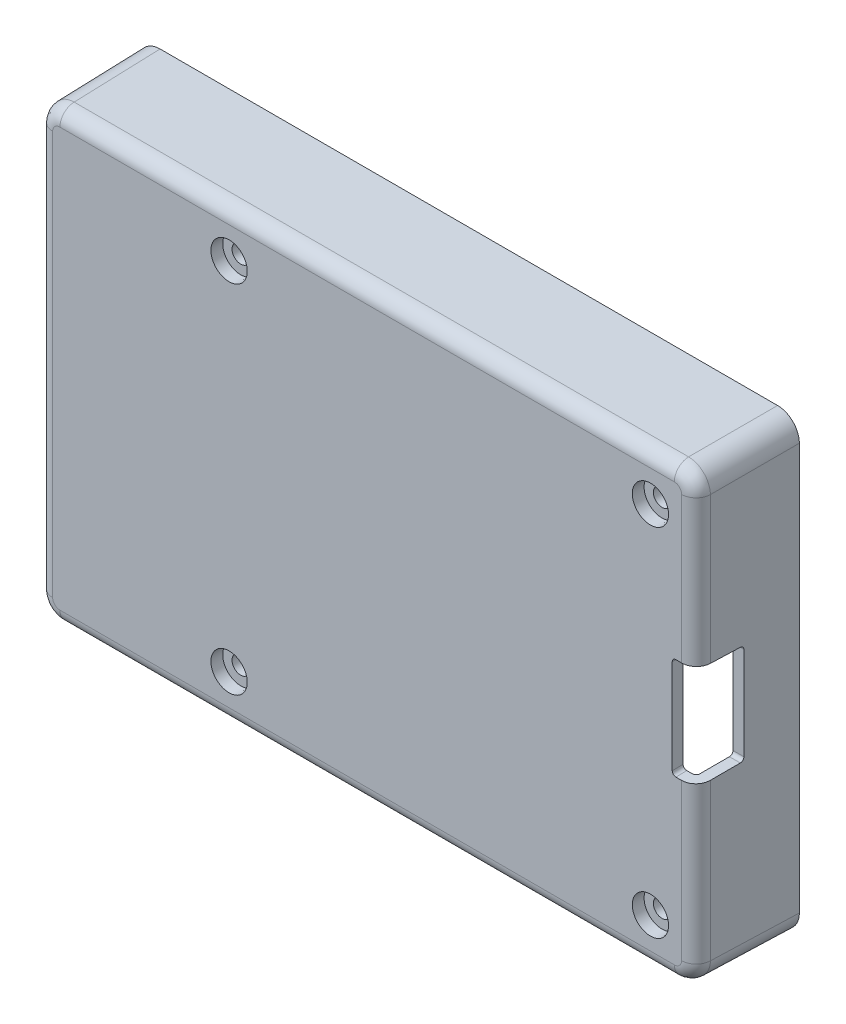
SolidWorks part; units mm, degrees
ref_plane "Front" through (0, 0, 0) normal (0, 0, 1) x (1, 0, 0)
ref_plane "Top" through (0, 0, 0) normal (0, 1, 0) x (1, 0, 0)
ref_plane "Right" through (0, 0, 0) normal (1, 0, 0) x (0, 0, -1)
sketch "Sketch1" plane through (0, 0, 0) normal (0, 0, 1) x (1, 0, 0)
  circle A0 centre (-19, 24.5) radius 3.5
  circle A1 centre (39, 24.5) radius 3.5
  circle A2 centre (-19, -24.5) radius 3.5
  circle A3 centre (39, -24.5) radius 3.5
  dimension "D1" = 7
extrude "Standoffs" add sketch "Sketch1" along normal blind 6 draft 1 draft outward yes
sketch "Sketch2" plane through (0, 0, 6) normal (0, 0, 1) x (1, 0, 0)
  line L1 (-45.5, 31) -> (45.5, 31)
  line L2 (-45.5, 31) -> (-45.5, -31)
  line L3 (-45.5, -31) -> (45.5, -31)
  line L4 (45.5, 31) -> (45.5, -31)
  line L5 (-45.5, 31) -> (45.5, -31) construction
  line L6 (-45.5, -31) -> (45.5, 31) construction
  line L9 (-40, 28) -> (40, 28) construction
  line L10 (42.5, 25.5) -> (42.5, -25.5) construction
  point P0 (0, 0)
  dimension "D1" = 3
  dimension "D2" = 3
extrude "Base" add sketch "Sketch2" against normal blind 1.5
sketch "Sketch3" plane through (0, 0, 4.5) normal (0, 0, -1) x (-1, 0, 0)
  line L0 (-44, 29.5) -> (-44, -29.5)
  line L1 (-44, -29.5) -> (44, -29.5)
  line L2 (44, -29.5) -> (44, 29.5)
  line L3 (44, 29.5) -> (-44, 29.5)
  line L4 (-45.5, 31) -> (-45.5, -31)
  line L5 (-45.5, -31) -> (45.5, -31)
  line L6 (45.5, -31) -> (45.5, 31)
  line L7 (45.5, 31) -> (-45.5, 31)
  line L8 (-45.5, 31) -> (-45.5, -31)
  line L9 (-45.5, -31) -> (45.5, -31)
  line L10 (45.5, -31) -> (45.5, 31)
  line L11 (45.5, 31) -> (-45.5, 31)
  dimension "D1" = 0
  dimension "D2" = 1.5
extrude "Walls" add sketch "Sketch3" along normal blind 12.5
hole_wizard "CBORE for M2 Pan Head Machine Screw1" positions "Sketch5" profile "Sketch6" counterbore size "M2" standard "ANSI Metric" end condition through all
sketch "Sketch5" plane through (0, 0, 6) normal (0, 0, 1) x (1, 0, 0)
  point P0 (39, -24.5)
  point P2 (-19, -24.5)
  point P4 (39, 24.5)
  point P6 (-19, 24.5)
sketch "Sketch6" plane through (39, -24.5, 6) normal (1, 0, 0) x (0, -1, 0)
  line L0 (0, 0) -> (0, 14)
  line L1 (0, 14) -> (1.2, 14)
  line L3 (1.2, 14) -> (1.2, 1.6)
  line L4 (1.2, 1.6) -> (2.5, 1.6)
  line L5 (2.5, 1.6) -> (2.5, 0)
  line L7 (2.5, 0) -> (0, 0)
  line L11 (0, -6.35) -> (0, 107.95) construction
  dimension "Thru Hole Dia." = 2.4
  dimension "Thru Hole Depth" = 14
  dimension "C'Bore Dia." = 5
  dimension "C'Bore Depth" = 1.6
sketch "Sketch7" plane through (0, 0, 0) normal (1, 0, 0) x (0, 0, -1)
  line L4 (1.6, -26) -> (15.8, -26)
  line L5 (15.8, -26) -> (15.8, -8.696)
  line L6 (15.8, -8.696) -> (1.6, -8.696)
  line L7 (1.6, -8.696) -> (1.6, -26)
  line L8 (1.6, -26) -> (15.8, -26)
  line L9 (15.8, -26) -> (15.8, -8.696)
  line L10 (15.8, -8.696) -> (1.6, -8.696)
  line L11 (1.6, -8.696) -> (1.6, -26)
  line L12 (0.81, -6.14) -> (17.3, -6.14)
  line L13 (17.3, -6.14) -> (17.3, 8.64)
  line L14 (17.3, 8.64) -> (0.81, 8.64)
  line L15 (0.81, 8.64) -> (0.81, -6.14)
  line L16 (0.81, -6.14) -> (17.3, -6.14)
  line L17 (17.3, -6.14) -> (17.3, 8.64)
  line L18 (17.3, 8.64) -> (0.81, 8.64)
  line L19 (0.81, 8.64) -> (0.81, -6.14)
  line L20 (0.81, 11.4) -> (17.3, 11.4)
  line L21 (17.3, 11.4) -> (17.3, 26.3)
  line L22 (17.3, 26.3) -> (0.81, 26.3)
  line L23 (0.81, 26.3) -> (0.81, 11.4)
  line L24 (0.81, 11.4) -> (17.3, 11.4)
  line L25 (17.3, 11.4) -> (17.3, 26.3)
  line L26 (17.3, 26.3) -> (0.81, 26.3)
  line L27 (0.81, 26.3) -> (0.81, 11.4)
  dimension "D1" = 0
  dimension "D2" = 0
  dimension "D3" = 0
extrude "USB and Ethernet Cut" cut sketch "Sketch7" against normal through all
sketch "Sketch8" plane through (0, 0, 0) normal (0, 1, 0) x (1, 0, 0)
  line L0 (10.2, 7.8) -> (10.2, 2.215) construction
  line L1 (12.32, 7.8) -> (8.08, 7.8) construction
  line L2 (10.075, 2.215) -> (10.325, 2.215) construction
  line L3 (2.7, 6.2) -> (2.7, 7) construction
  line L4 (2.2, 1.3) -> (18.2, 1.3)
  line L5 (2.2, 1.3) -> (2.2, 8.715)
  line L6 (2.2, 8.715) -> (18.2, 8.715)
  line L7 (18.2, 1.3) -> (18.2, 8.715)
  line L8 (2.2, 1.3) -> (18.2, 8.715) construction
  line L9 (2.2, 8.715) -> (18.2, 1.3) construction
  line L10 (31.75, 4.1369) -> (31.75, 1.3) construction
  line L11 (34.75, 4.1369) -> (28.75, 4.1369) construction
  line L12 (-40, 1.3) -> (40, 1.3) construction
  line L13 (28.01, 2.6036) -> (28.01, 3.35) construction
  line L14 (27.51, 0.8075) -> (35.99, 0.8075)
  line L15 (27.51, 0.8075) -> (27.51, 4.6294)
  line L16 (27.51, 4.6294) -> (35.99, 4.6294)
  line L17 (35.99, 0.8075) -> (35.99, 4.6294)
  line L18 (27.51, 0.8075) -> (35.99, 4.6294) construction
  line L19 (27.51, 4.6294) -> (35.99, 0.8075) construction
  line L20 (28.75, 4.1294) -> (34.75, 4.1294) construction
  line L21 (-14.4, 4.3) -> (-14.4646, 8)
  line L22 (45.5, 8) -> (-45.5, 8) construction
  line L23 (-14.4646, 8) -> (-7.3354, 8)
  line L24 (-10.9, 8) -> (-10.9, 4.3) construction
  line L25 (-7.4, 4.3) -> (-7.3354, 8)
  line L26 (27.51, 4.6294) -> (27.51, 8)
  line L27 (27.51, 8) -> (35.99, 8)
  line L28 (35.99, 8) -> (35.99, 4.6294)
  circle A0 centre (-10.9, 4.3) radius 3.5
  arc A1 (-9.9633, 7.15) -> (-11.8367, 7.15) centre (-10.9, 4.3) ccw construction
  point P12 (10.2, 5.0075)
  point P26 (31.75, 2.7184)
  dimension "D1" = 0.5
  dimension "D2" = 0.5
  dimension "D3" = 1.3
  dimension "D4" = 0.5
  dimension "D5" = 0.5
  dimension "D6" = 89
extrude "Side Ports" cut sketch "Sketch8" against normal through all contours L28 L27 L26 L16 | L14 L17 L16 L15 | L4 L7 L6 L5 | A0 L25 L23 L21 | A0 L23
draft "Draft2" type of draft neutral plane draft angle 1 faces to draft 4 face at (0, 31, -1) face at (-45.5, 0.688, -3.6525) face at (45.5, 0, -1) face at (7.7625, -31, -3.8322) neutral plane through (0, 0, -8) neutral plane normal (0, 0, -1) reverse direction yes parameters "D1"=1
draft "Draft3" type of draft neutral plane draft angle 1 faces to draft 4 face at (44, 0, -1.75) face at (0, 29.5, -1.75) face at (-44, 0.688, -3.84) face at (7.7625, -29.5, -4.0197) neutral plane through (0, 0, -8) neutral plane normal (0, 0, -1) parameters "D1"=1
fillet "Fillet1" radius 3 4 edges at (-45.3778, 30.8778, -1) (-45.3778, -30.8778, -1) (45.3778, 30.8778, -1) (45.3778, -30.8778, -1)
fillet "Fillet2" radius 1.5 4 edges at (-43.8909, -29.3909, -1.75) (-43.8909, 29.3909, -1.75) (43.8909, 29.3909, -1.75) (43.8909, -29.3909, -1.75)
fillet "Fillet3" radius 2 8 edges at (-44.3771, -29.8771, 6) (-45.2556, 0, 6) (-44.3771, 29.8771, 6) (0, 30.7556, 6) (44.3771, 29.8771, 6) (45.2556, 0, 6) (44.3771, -29.8771, 6) (0, -30.7556, 6)
fillet "Fillet4" radius 0.5 12 edges at (-15.4215, 24.5, 4.5) (42.5785, 24.5, 4.5) (-15.4215, -24.5, 4.5) (42.5785, -24.5, 4.5) (43.3426, -28.8426, 4.5) (43.7818, 0, 4.5) (43.3426, 28.8426, 4.5) (0, 29.2818, 4.5) (-43.3426, 28.8426, 4.5) (-43.7818, 0, 4.5) (-43.3426, -28.8426, 4.5) (0, -29.2818, 4.5)
sketch "Sketch10" plane through (0, 0, 0) normal (1, 0, 0) x (0, 0, -1)
  line L0 (-0.65, 7.2) -> (-0.65, -5.8) construction
  line L1 (-1.3, 7.2) -> (0, 7.2) construction
  line L2 (-1.3, -5.8) -> (0, -5.8) construction
  line L3 (-1.3, 7.2) -> (-1.3, -5.8) construction
  line L4 (0.5, -6.3) -> (-1.8, -6.3)
  line L5 (0.5, -6.3) -> (0.5, 7.7)
  line L6 (0.5, 7.7) -> (-1.8, 7.7)
  line L7 (-1.8, -6.3) -> (-1.8, 7.7)
  line L8 (0.5, -6.3) -> (-1.8, 7.7) construction
  line L9 (0.5, 7.7) -> (-1.8, -6.3) construction
  line L10 (-1.8, 7.7) -> (-6, 7.7)
  line L11 (-6, -30.7556) -> (-6, 30.7556) construction
  line L12 (-6, 7.7) -> (-6, -6.3)
  line L13 (-6, -6.3) -> (-1.8, -6.3)
  point P6 (-0.65, 0.7)
  dimension "D1" = 0.5
  dimension "D2" = 0.5
extrude "SD Card" cut sketch "Sketch10" along normal through all from offset 42 contours L7 L4 L5 L6 | L12 L13 L7 L10
draft "Draft4" type of draft neutral plane draft angle 1 faces to draft 10 face at (2.2, -30.1915, -4.65) face at (27.51, -30.1872, -4.4038) face at (35.99, -30.1872, -4.4038) face at (18.2, -30.1915, -4.65) face at (-44.6941, -26, -4.8) face at (-44.6872, -6.14, -4.405) face at (-44.6872, 11.4, -4.405) face at (-44.6941, -8.696, -4.8) face at (-44.6872, 8.64, -4.405) face at (-44.6872, 26.3, -4.405) neutral plane through (0, 0, -8) neutral plane normal (0, 0, -1) parameters "D1"=1
draft "Draft7" type of draft neutral plane draft angle 1 faces to draft 2 face at (43.6752, -6.3, 3.5694) face at (43.6752, 7.7, 3.5694) neutral plane through (-19, 24.5, 6) neutral plane normal (0, 0, 1) parameters "D1"=1
draft "Draft8" type of draft neutral plane draft angle 1 faces to draft 4 parameters "D1"=1
fillet "Fillet5" radius 1 4 edges at (2.3169, -30.1331, -1.3) (18.0831, -30.1331, -1.3) (27.6355, -30.1245, -0.8075) (35.8645, -30.1245, -0.8075)
fillet "Fillet6" radius 0.5 10 edges at (42, -6.2869, 5.25) (44.6191, -6.1865, -0.5) (44.6191, 7.5865, -0.5) (42, 7.6869, 5.25) (-44.6245, 26.1745, -0.81) (-44.6245, 11.5255, -0.81) (-44.6245, 8.5145, -0.81) (-44.6245, -6.0145, -0.81) (-44.6383, -8.8077, -1.6) (-44.6383, -25.8883, -1.6)
